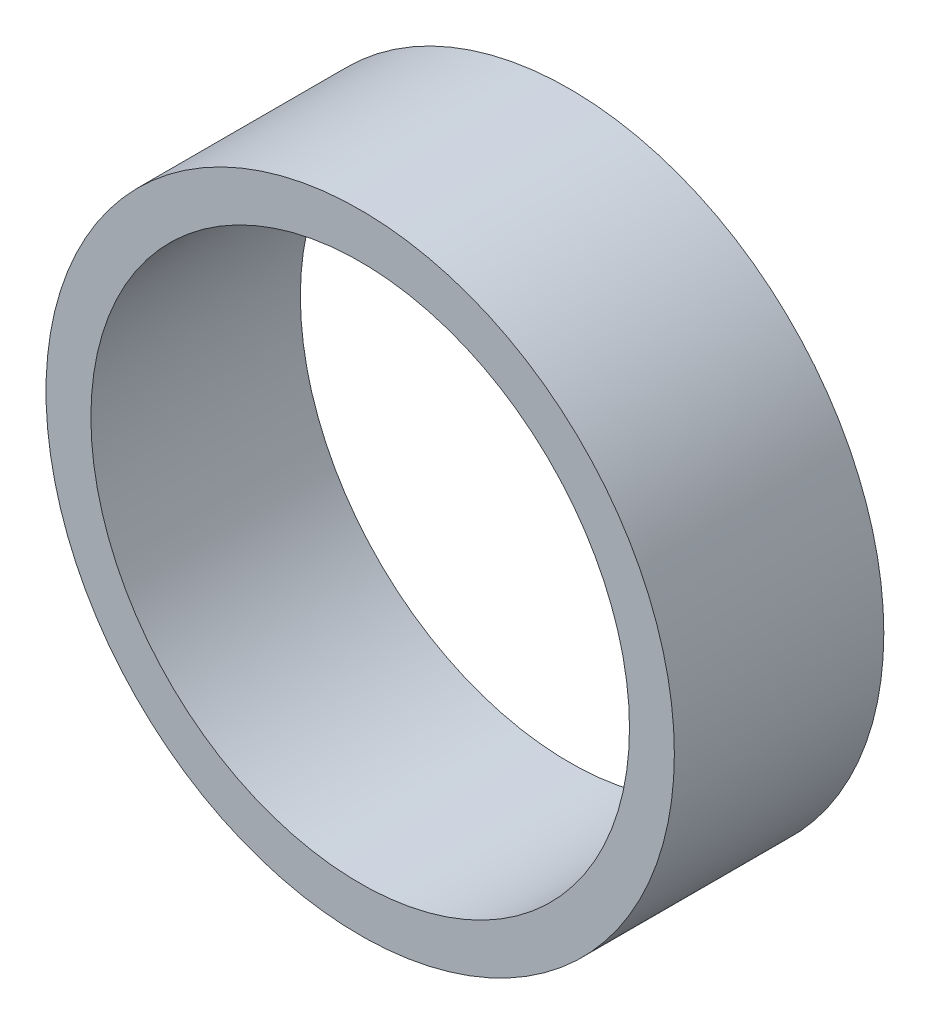
SolidWorks part; units mm, degrees
material "SBR"
ref_plane "Front Plane" through (0, 0, 0) normal (0, 0, 1) x (1, 0, 0)
ref_plane "Top Plane" through (0, 0, 0) normal (0, 1, 0) x (1, 0, 0)
ref_plane "Right Plane" through (0, 0, 0) normal (1, 0, 0) x (0, 0, -1)
sketch "Sketch1" plane through (0, 0, 0) normal (0, 0, 1) x (1, 0, 0)
  circle A0 centre (0, 0) radius 266.7
  circle A1 centre (0, 0) radius 228.6
extrude "Boss-Extrude1" add sketch "Sketch1" along normal blind 177.8
